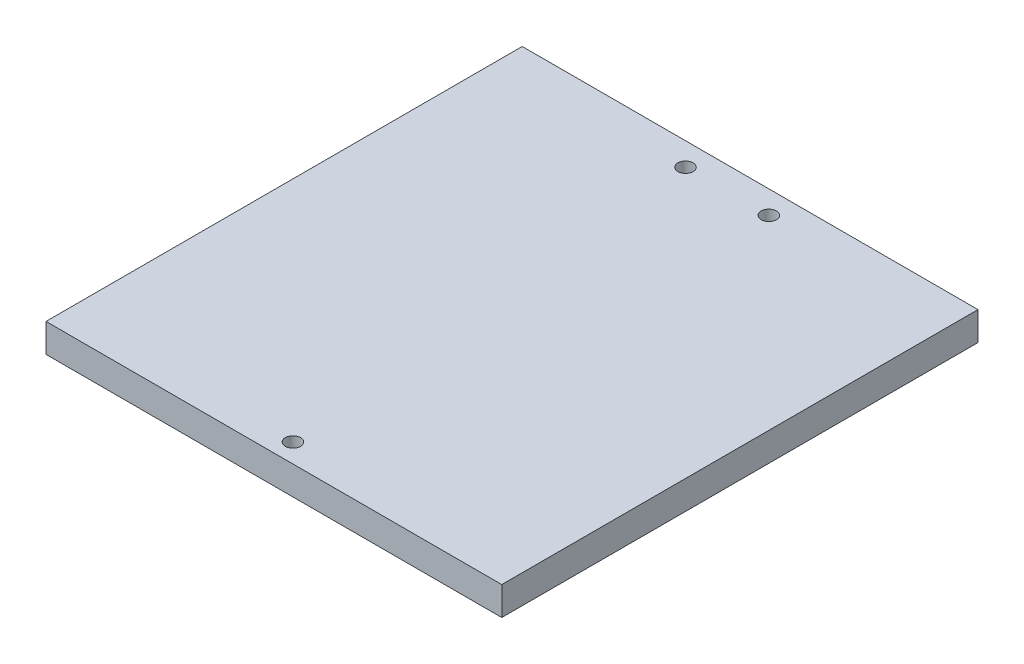
SolidWorks part; units mm, degrees
ref_plane "Front Plane" through (0, 0, 0) normal (0, 0, 1) x (1, 0, 0)
ref_plane "Top Plane" through (0, 0, 0) normal (0, 1, 0) x (1, 0, 0)
ref_plane "Right Plane" through (0, 0, 0) normal (1, 0, 0) x (0, 0, -1)
sketch "Sketch1" plane through (0, 0, 0) normal (0, 1, 0) x (1, 0, 0)
  line L0 (0, 49.8437) -> (0, -62.7125) construction
  line L1 (-73.7687, 0) -> (75.7625, 0) construction
  line L3 (-47.85, -50) -> (47.85, -50)
  line L4 (-47.85, -50) -> (-47.85, 50)
  line L5 (-47.85, 50) -> (47.85, 50)
  line L6 (47.85, -50) -> (47.85, 50)
  line L7 (-47.85, -50) -> (47.85, 50) construction
  line L8 (-47.85, 50) -> (47.85, -50) construction
  circle A0 centre (-8.75, 45.1814) radius 1.6
  circle A1 centre (8.75, 45.1814) radius 1.6
  circle A2 centre (0, -46) radius 1.6
  point P4 (0, 0)
  dimension "D3" = 3.2
  dimension "D5" = 3.2
  dimension "D1" = 95.7
  dimension "D2" = 100
  dimension "D4" = 17.5
  dimension "D6" = 4
extrude "Boss-Extrude1" add sketch "Sketch1" along normal mid plane 6
